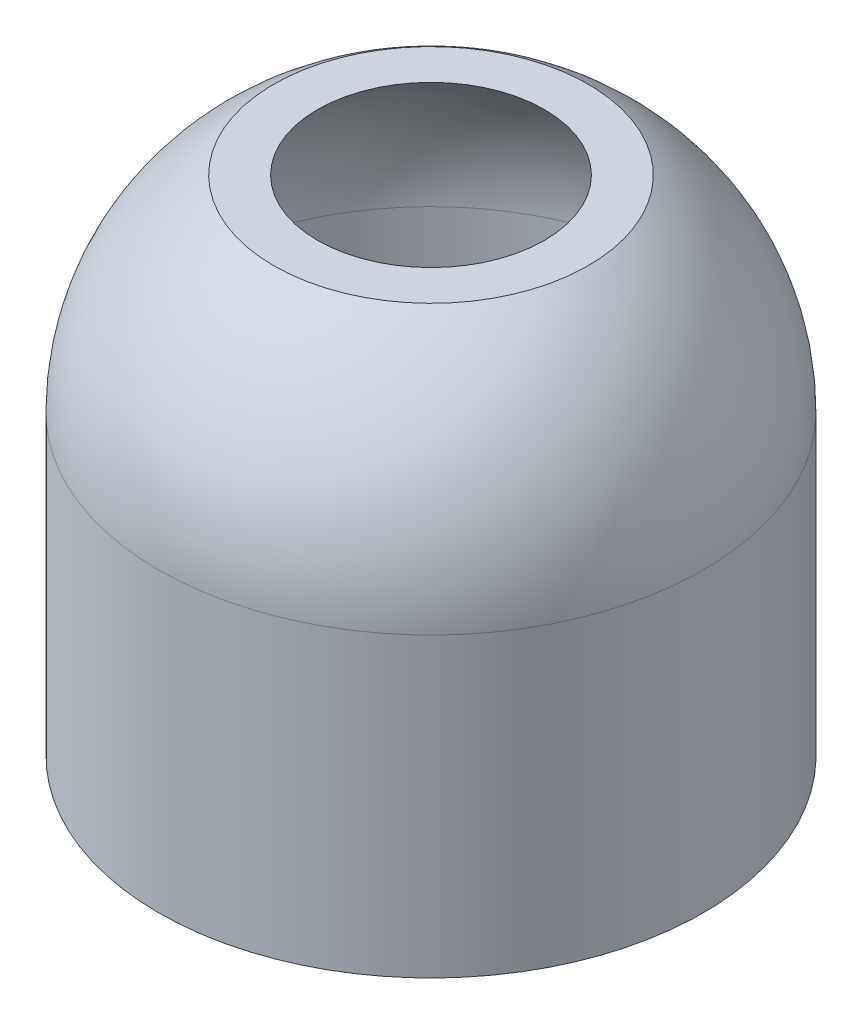
SolidWorks part; units mm, degrees
material "Wrought Stainless Steel"
ref_plane "Front Plane" through (0, 0, 0) normal (0, 0, 1) x (1, 0, 0)
ref_plane "Top Plane" through (0, 0, 0) normal (0, 1, 0) x (1, 0, 0)
ref_plane "Right Plane" through (0, 0, 0) normal (1, 0, 0) x (0, 0, -1)
sketch "Sketch3" plane through (0, 0, 0) normal (0, 0, 1) x (1, 0, 0)
  line L0 (0, 50.3699) -> (0, 0) construction
  line L1 (27.5, 0) -> (27.5, 30)
  line L2 (25.5, 0) -> (25.5, 30)
  line L3 (15.88, 50.8) -> (11.4579, 50.8)
  line L4 (27.5, 0) -> (25.5, 0)
  arc A0 (27.5, 30) -> (15.88, 50.8) centre (3.0738, 30) ccw
  arc A1 (25.5, 30) -> (11.4579, 50.8) centre (3.0738, 30) ccw
  arc A2 (25.5, 30) -> (14.8314, 49.0969) centre (3.0738, 30) ccw construction
  dimension "D1" = 27.5
  dimension "D2" = 30
  dimension "D3" = 50.8
  dimension "D4" = 15.88
  dimension "D5" = 2
revolve "Revolve1" add sketch "Sketch3" angle 360 about L0
